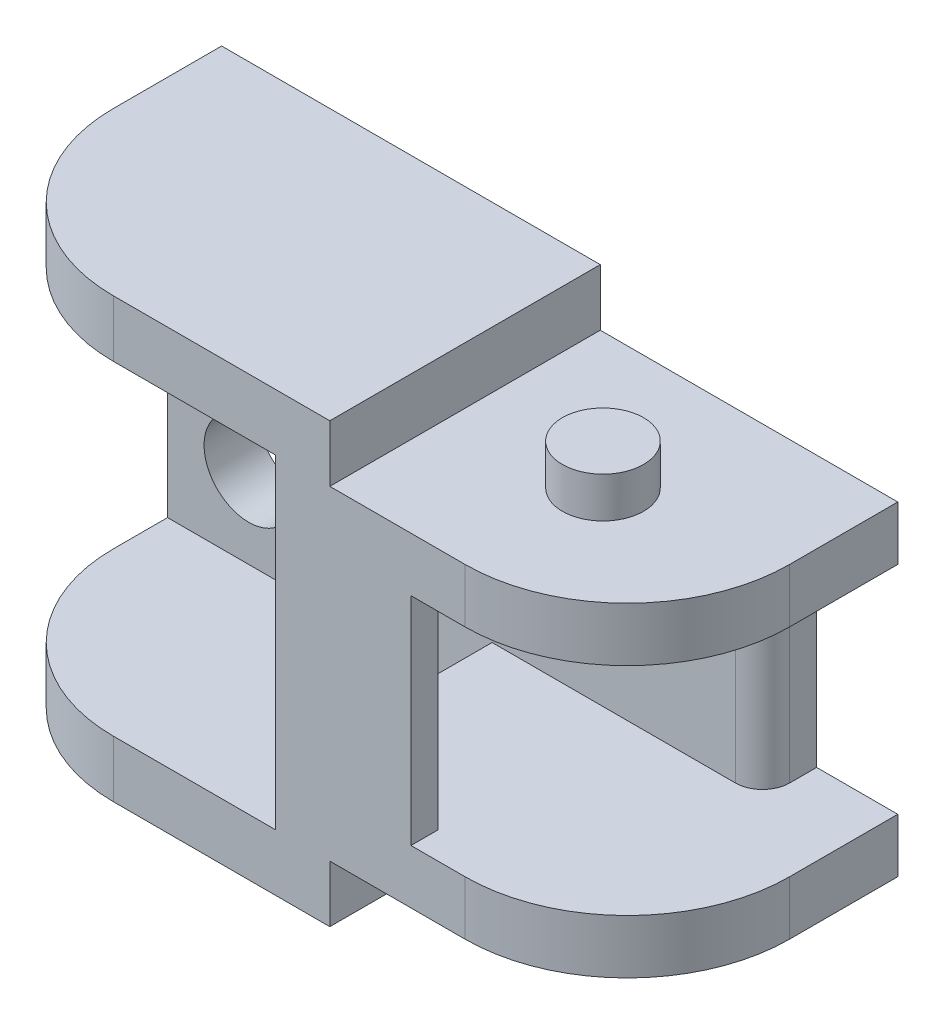
SolidWorks part; units mm, degrees
material "Сталь 45 ГОСТ 1050-2013"
ref_plane "Спереди" through (0, 0, 0) normal (0, 0, 1) x (1, 0, 0)
ref_plane "Сверху" through (0, 0, 0) normal (0, 1, 0) x (1, 0, 0)
ref_plane "Справа" through (0, 0, 0) normal (1, 0, 0) x (0, 0, -1)
sketch "Эскиз2" plane through (0, 0, 0) normal (0, 0, 1) x (1, 0, 0)
  line L0 (0, 0) -> (0, 2)
  line L1 (0, 2) -> (13, 2)
  line L2 (13, 2) -> (13, -0.1)
  line L3 (13, -0.1) -> (24, -0.1)
  line L4 (24, -0.1) -> (24, -2.1)
  line L5 (24, -2.1) -> (11, -2.1)
  line L6 (11, -2.1) -> (11, 0)
  line L7 (11, 0) -> (0, 0)
  dimension "D1" = 2
  dimension "D2" = 24
  dimension "D3" = 2
  dimension "D4" = 11
  dimension "D5" = 0.1
  dimension "D6" = 2
extrude "Бобышка-Вытянуть2" add sketch "Эскиз2" along normal blind 10
sketch "Эскиз3" plane through (0, -0.1, 0) normal (0, 1, 0) x (1, 0, 0)
  line L0 (0, -10) -> (0, 0) construction
  line L1 (24, -10) -> (24, 0) construction
  circle A0 centre (6, -5) radius 1.5 construction
  circle A1 centre (18.1, -5) radius 1.5
  point P5 (0, -5)
  dimension "D1" = 3
  dimension "D2" = 5.9
  dimension "D3" = 6
extrude "Бобышка-Вытянуть3" add sketch "Эскиз3" along normal blind 1.5
sketch "Эскиз5" plane through (0, 0, 0) normal (0, -1, 0) x (1, 0, 0)
  line L0 (0, 10) -> (0, 0) construction
  circle A0 centre (5, 5) radius 1.65
  point P2 (0, 5)
  dimension "D1" = 3.3
  dimension "D2" = 5
extrude "Вырез-Вытянуть2" cut sketch "Эскиз5" against normal through all
fillet "Скругление1" radius 6 2 edges at (24, -1.1, 10) (0, 1, 10)
sketch "Эскиз6" plane through (0, -2.1, 0) normal (0, -1, 0) x (-1, 0, 0)
  line L1 (-11, 0) -> (-21, 0)
  line L2 (-11, 0) -> (-11, -1)
  line L3 (-11, -1) -> (-21, -1)
  line L4 (-21, 0) -> (-21, -1)
  line L5 (-11, 0) -> (-21, -1) construction
  line L6 (-11, -1) -> (-21, 0) construction
  line L7 (-11, -9) -> (-16, -9)
  line L8 (-11, -9) -> (-11, -10)
  line L9 (-11, -10) -> (-16, -10)
  line L10 (-16, -9) -> (-16, -10)
  line L11 (-11, -9) -> (-16, -10) construction
  line L12 (-11, -10) -> (-16, -9) construction
  point P0 (-16, -0.5)
  point P5 (-13.5, -9.5)
  dimension "D1" = 1
  dimension "D2" = 10
  dimension "D3" = 5
extrude "Бобышка-Вытянуть4" add sketch "Эскиз6" along normal blind 4
sketch "Эскиз7" plane through (0, 0, 0) normal (0, -1, 0) x (1, 0, 0)
  line L1 (-0.6896, 3.35) -> (5, 3.35)
  line L2 (-0.6896, 3.35) -> (-0.6896, 6.65)
  line L3 (-0.6896, 6.65) -> (5, 6.65)
  line L4 (5, 3.35) -> (5, 6.65)
  line L5 (-0.6896, 3.35) -> (5, 6.65) construction
  line L6 (-0.6896, 6.65) -> (5, 3.35) construction
  circle A0 centre (5, 5) radius 1.65 construction
  point P0 (2.1552, 5)
extrude "Вырез-Вытянуть3" cut sketch "Эскиз7" against normal blind 0.5
mirror "Зеркальное отражение1" about plane through (0, -6.1, 0) normal (0, 1, 0) of bodies 111 109
sketch "Эскиз8" plane through (0, 0, 10) normal (0, 0, 1) x (1, 0, 0)
  line L0 (11, 0) -> (11, -12.2) construction
  line L1 (-0.3065, -16.1301) -> (11, -16.1301)
  line L2 (-0.3065, -16.1301) -> (-0.3065, 2.9125)
  line L3 (-0.3065, 2.9125) -> (11, 2.9125)
  line L4 (11, -16.1301) -> (11, 2.9125)
  line L5 (-0.3065, -16.1301) -> (11, 2.9125) construction
  line L6 (-0.3065, 2.9125) -> (11, -16.1301) construction
  point P0 (5.3467, -6.6088)
extrude "Вырез-Вытянуть4" cut sketch "Эскиз8" against normal through all
other "Переместить грань1" face at (11, -6.1, 5) parameters "D1"=12
sketch "Эскиз9" plane through (0, 0, 10) normal (0, 0, 1) x (1, 0, 0)
  line L0 (18, -0.1) -> (13, -0.1) construction
  line L1 (-3.1884, -12.1) -> (11, -12.1)
  line L2 (-3.1884, -12.1) -> (-3.1884, -0.1)
  line L3 (-3.1884, -0.1) -> (11, -0.1)
  line L4 (11, -12.1) -> (11, -0.1)
  line L5 (-3.1884, -12.1) -> (11, -0.1) construction
  line L6 (-3.1884, -0.1) -> (11, -12.1) construction
  line L7 (18, -12.1) -> (13, -12.1) construction
  line L8 (13, -0.1) -> (13, 2) construction
  point P0 (3.9058, -6.1)
  point P11 (-3.1884, 0)
  dimension "D1" = 2
extrude "Вырез-Вытянуть5" cut sketch "Эскиз9" against normal up to surface (9 mm away) up to face at (10, -6.1, 1)
sketch "Эскиз10" plane through (0, 0, 1) normal (0, 0, 1) x (1, 0, 0)
  line L0 (-1, -6.1) -> (49999, -6.1) construction
  line L1 (-1, -12.1) -> (-1, -0.1) construction
  line L2 (5, -0.1) -> (5, -50000.1) construction
  line L3 (11, -0.1) -> (-1, -0.1) construction
  circle A0 centre (2, -9.1) radius 1.65
  circle A1 centre (8, -3.1) radius 1.65
  point P4 (-1, -6.1)
  point P9 (5, -0.1)
  dimension "D1" = 3.3
  dimension "D2" = 3.3
  dimension "D3" = 3
  dimension "D4" = 3
  dimension "D5" = 3
  dimension "D6" = 3
extrude "Вырез-Вытянуть6" cut sketch "Эскиз10" against normal through all
fillet "Скругление2" radius 6 2 edges at (-1, -13.15, 10) (-1, 0.95, 10)
other "Переместить грань2" face at (3.65, -9.1, 1) parameters "D1"=1
fillet "Скругление3" radius 1 1 edges at (21, -6.1, 2)
